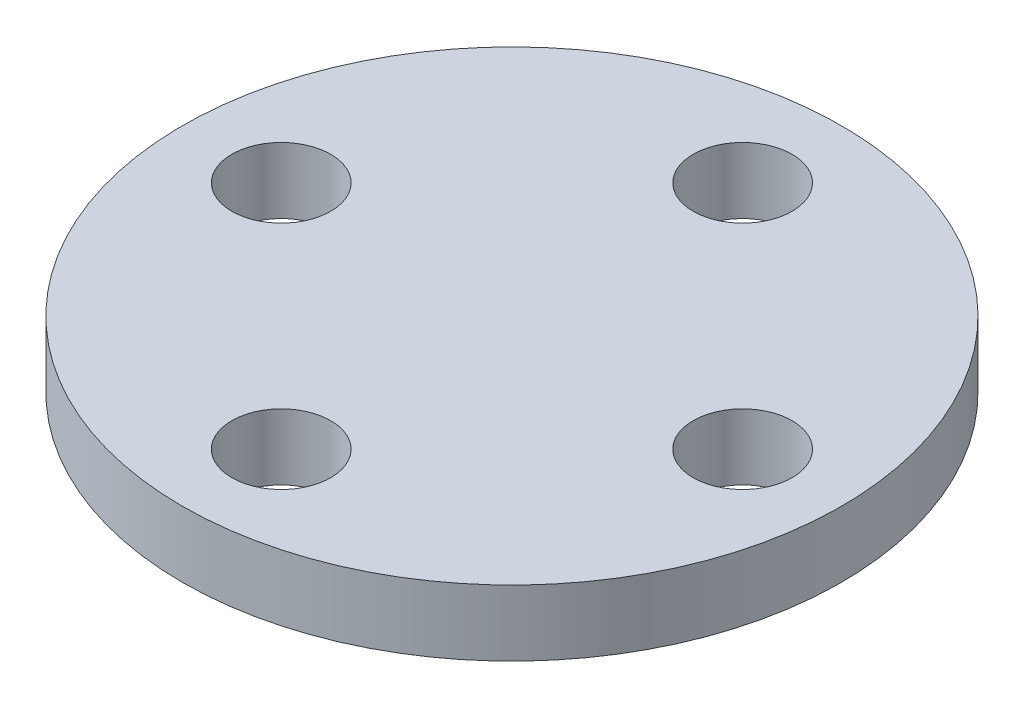
SolidWorks part; units mm, degrees
ref_plane "Front Plane" through (0, 0, 0) normal (0, 0, 1) x (1, 0, 0)
ref_plane "Top Plane" through (0, 0, 0) normal (0, 1, 0) x (1, 0, 0)
ref_plane "Right Plane" through (0, 0, 0) normal (1, 0, 0) x (0, 0, -1)
sketch "Sketch1" plane through (0, 0, 0) normal (0, 1, 0) x (1, 0, 0)
  circle A1 centre (0, 0) radius 10
  circle A2 centre (0, 7) radius 1.5
  circle A3 centre (7, 0) radius 1.5
  circle A4 centre (0, -7) radius 1.5
  circle A5 centre (-7, 0) radius 1.5
  dimension "D1" = 3
  dimension "D2" = 3
  dimension "D3" = 3
  dimension "D4" = 3
  dimension "D5" = 7
  dimension "D6" = 20
  dimension "D7" = 7
  dimension "D8" = 7
  dimension "D9" = 7
extrude "Boss-Extrude1" add sketch "Sketch1" along normal blind 2
sketch "Sketch2" plane through (0, 0, 0) normal (0, -1, 0) x (1, 0, 0)
  circle A0 centre (0, 0) radius 4
  circle A1 centre (0, 0) radius 2
  dimension "D1" = 8
  dimension "D2" = 4
extrude "Boss-Extrude2" add sketch "Sketch2" along normal blind 3
